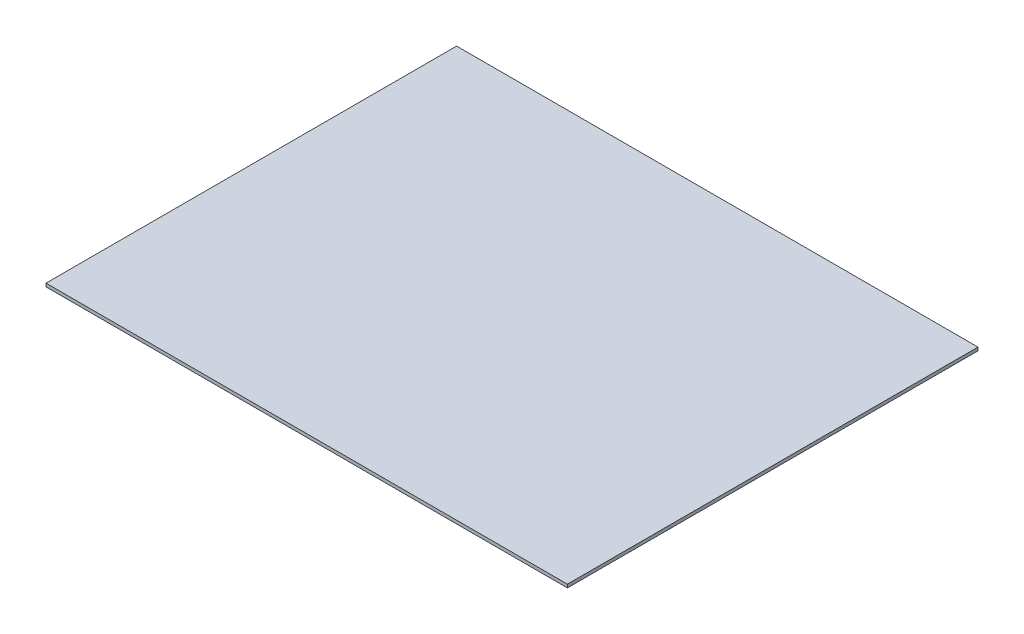
SolidWorks part; units mm, degrees
ref_plane "Front" through (0, 0, 0) normal (0, 0, 1) x (1, 0, 0)
ref_plane "Top" through (0, 0, 0) normal (0, 1, 0) x (1, 0, 0)
ref_plane "Right" through (0, 0, 0) normal (1, 0, 0) x (0, 0, -1)
sketch "Sketch1" plane through (0, 0, 0) normal (0, 1, 0) x (1, 0, 0)
  line L1 (0, 0) -> (2032, 0)
  line L2 (0, 0) -> (0, 1600.2)
  line L3 (0, 1600.2) -> (2032, 1600.2)
  line L4 (2032, 0) -> (2032, 1600.2)
  dimension "D1" = 1600.2
  dimension "D2" = 2032
extrude "Boss-Extrude1" add sketch "Sketch1" along normal blind 12.7
